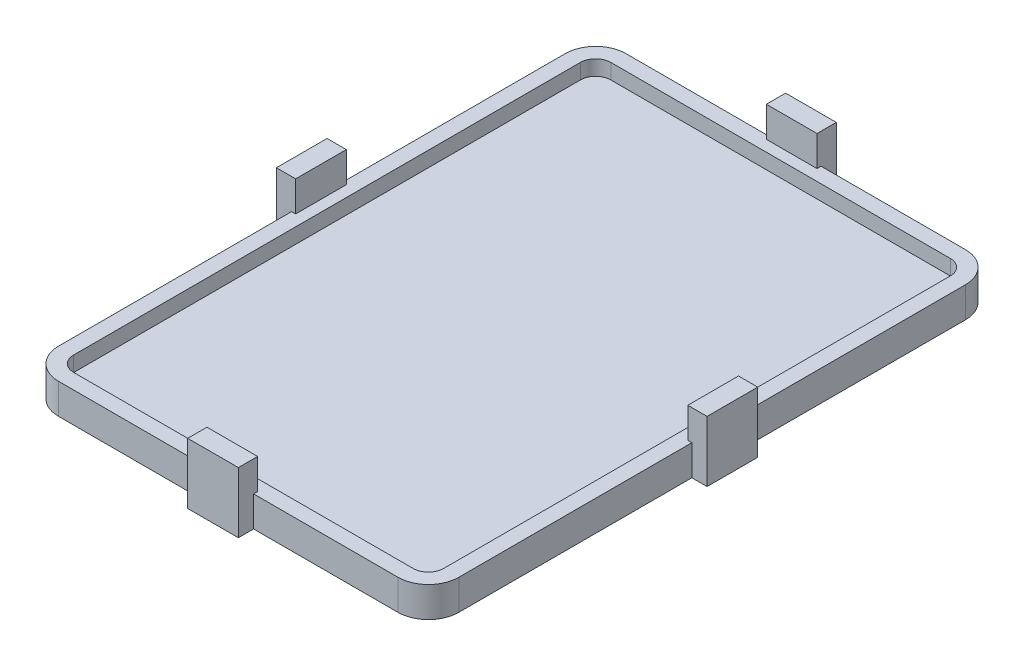
SolidWorks part; units mm, degrees
ref_plane "Front Plane" through (0, 0, 0) normal (0, 0, 1) x (1, 0, 0)
ref_plane "Top Plane" through (0, 0, 0) normal (0, 1, 0) x (1, 0, 0)
ref_plane "Right Plane" through (0, 0, 0) normal (1, 0, 0) x (0, 0, -1)
sketch "Sketch1" plane through (0, 0, 0) normal (0, 1, 0) x (1, 0, 0)
  line L1 (0, 0) -> (39.5, 0)
  line L2 (0, 0) -> (0, 56)
  line L3 (0, 56) -> (39.5, 56)
  line L4 (39.5, 0) -> (39.5, 56)
  dimension "D1" = 39.5
  dimension "D2" = 56
extrude "Boss-Extrude1" add sketch "Sketch1" along normal blind 3
fillet "Fillet1" radius 3 4 edges at (0, 1.5, 0) (39.5, 1.5, 0) (39.5, 1.5, -56) (0, 1.5, -56)
shell "Shell1" thickness 1.5
sketch "Sketch2" plane through (0, 0, 0) normal (-1, 0, 0) x (0, 0, 1)
  line L0 (-53, 0) -> (-3, 0) construction
  line L1 (-31, 3) -> (-26, 3)
  line L2 (-31, 3) -> (-31, 0)
  line L3 (-31, 0) -> (-26, 0)
  line L4 (-26, 3) -> (-26, 0)
  line L5 (-56, 0) -> (-56, 3) construction
  point P6 (-56, 1.5)
  dimension "D1" = 5
  dimension "D2" = 3
  dimension "D3" = 0
  dimension "D4" = 25
extrude "Boss-Extrude2" add sketch "Sketch2" along normal blind 1.5
sketch "Sketch3" plane through (0, 3, 0) normal (0, 1, 0) x (1, 0, 0)
  line L0 (-1.5, 26) -> (-1.5, 31) construction
  line L1 (0.4, 31) -> (-1.5, 31)
  line L2 (0.4, 31) -> (0.4, 26)
  line L3 (0.4, 26) -> (-1.5, 26)
  line L4 (-1.5, 31) -> (-1.5, 26)
  line L5 (-1.5, 26) -> (0, 26) construction
  point P4 (-1.5, 28.5)
  dimension "D1" = 5
  dimension "D2" = 1.9
  dimension "D3" = 0
  dimension "D4" = 0
extrude "Boss-Extrude3" add sketch "Sketch3" along normal blind 3
ref_plane "Plane2" through (19.75, 0, 0) normal (1, 0, 0) x (0, 0, -1)
sketch "Sketch8" plane through (0, 0, 0) normal (0, 0, 1) x (1, 0, 0)
  line L0 (3, 0) -> (36.5, 0) construction
  line L1 (17.25, 3) -> (22.25, 3)
  line L2 (17.25, 3) -> (17.25, 0)
  line L3 (17.25, 0) -> (22.25, 0)
  line L4 (22.25, 3) -> (22.25, 0)
  line L5 (0, 0) -> (0, 3) construction
  dimension "D1" = 5
  dimension "D2" = 3
  dimension "D3" = 0
  dimension "D4" = 17.25
extrude "Boss-Extrude5" add sketch "Sketch8" along normal blind 1.5
sketch "Sketch9" plane through (0, 3, 0) normal (0, 1, 0) x (1, 0, 0)
  line L0 (22.25, -1.5) -> (17.25, -1.5) construction
  line L1 (17.25, 0.4) -> (22.25, 0.4)
  line L2 (17.25, 0.4) -> (17.25, -1.5)
  line L3 (17.25, -1.5) -> (22.25, -1.5)
  line L4 (22.25, 0.4) -> (22.25, -1.5)
  line L5 (22.25, -1.5) -> (22.25, 0) construction
  dimension "D1" = 1.9
  dimension "D2" = 5
  dimension "D3" = 0
  dimension "D4" = 0
extrude "Boss-Extrude6" add sketch "Sketch9" along normal blind 3
ref_plane "Plane3" through (0, 0, -28) normal (0, 0, -1) x (-1, 0, 0)
mirror "Mirror3" about plane through (19.75, 0, 0) normal (1, 0, 0) of "Boss-Extrude3", "Boss-Extrude2"
mirror "Mirror4" about plane through (0, 0, -28) normal (0, 0, -1) of "Boss-Extrude6", "Boss-Extrude5"
